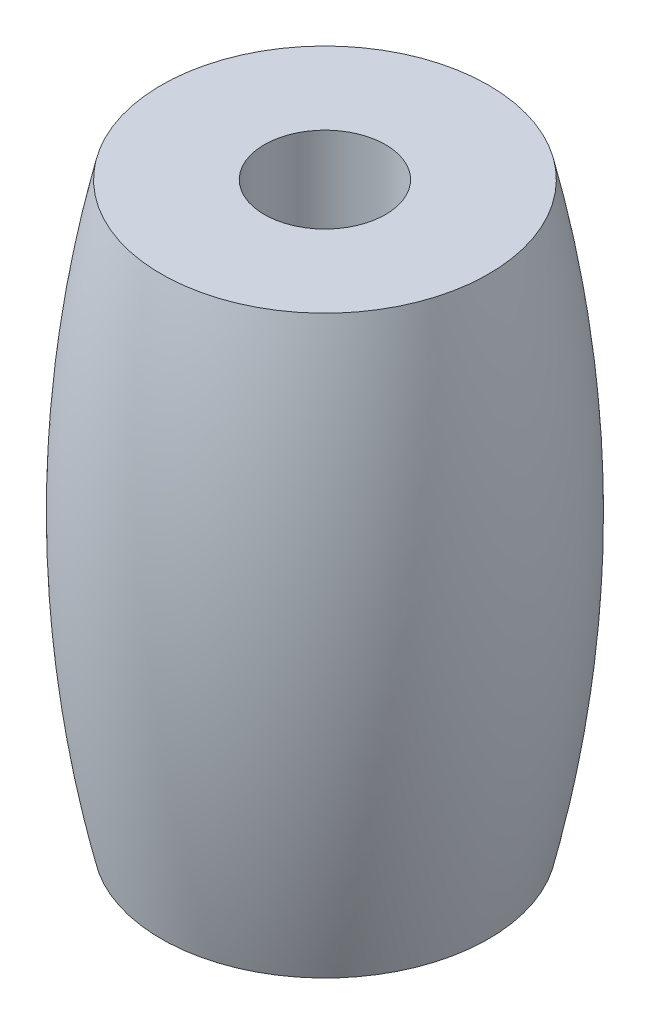
SolidWorks part; units mm, degrees
ref_plane "Alzado" through (0, 0, 0) normal (0, 0, 1) x (1, 0, 0)
ref_plane "Planta" through (0, 0, 0) normal (0, 1, 0) x (1, 0, 0)
ref_plane "Vista lateral" through (0, 0, 0) normal (1, 0, 0) x (0, 0, -1)
sketch "Croquis1" plane through (0, 0, 0) normal (0, 0, 1) x (1, 0, 0)
  line L0 (0, 0) -> (0, 19) construction
  line L1 (0, 19) -> (2, 19) construction
  line L2 (0, 0) -> (2, 0) construction
  line L3 (2, 19) -> (2, 0)
  line L4 (2, 9.5) -> (6.5, 9.5) construction
  line L5 (2, 19) -> (5.4, 19)
  line L6 (2, 0) -> (5.4, 0)
  spline S0 degree 2 poles (5.4, 19) (7.6, 9.5) (5.4, 0) knots 0 0 0 1 1 1
  dimension "D1" = 19
  dimension "D2" = 2
  dimension "D3" = 3.4
  dimension "D4" = 6.5
revolve "Revolución2" add sketch "Croquis1" angle 360 about L0
